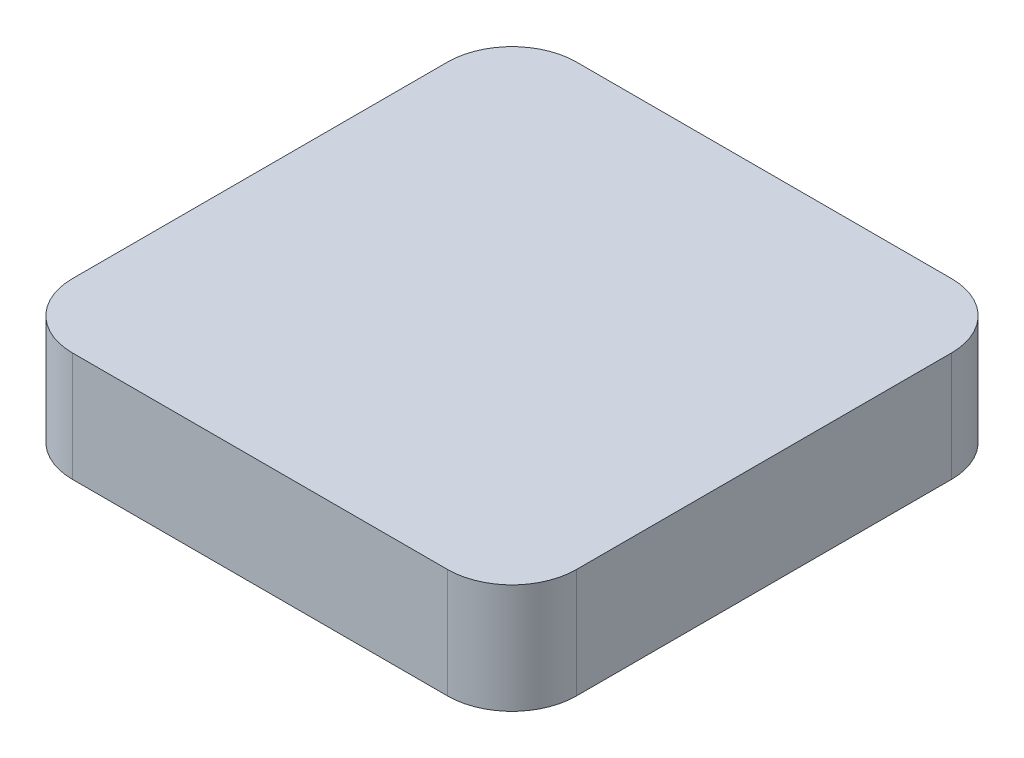
SolidWorks part; units mm, degrees
ref_plane "前视基准面" through (0, 0, 0) normal (0, 0, 1) x (1, 0, 0)
ref_plane "上视基准面" through (0, 0, 0) normal (0, 1, 0) x (1, 0, 0)
ref_plane "右视基准面" through (0, 0, 0) normal (1, 0, 0) x (0, 0, -1)
sketch "草图1" plane through (0, 0, 0) normal (0, 1, 0) x (1, 0, 0)
  line L1 (-28.9073, 18.1297) -> (10.1927, 18.1297)
  line L2 (-28.9073, 18.1297) -> (-28.9073, -20.9703)
  line L3 (-28.9073, -20.9703) -> (10.1927, -20.9703)
  line L4 (10.1927, 18.1297) -> (10.1927, -20.9703)
  line L5 (-28.9073, 18.1297) -> (10.1927, -20.9703) construction
  line L6 (-28.9073, -20.9703) -> (10.1927, 18.1297) construction
  point P0 (-9.3573, -1.4203)
  dimension "D1" = 39.1
  dimension "D2" = 39.1
extrude "凸台-拉伸1" add sketch "草图1" along normal blind 8.5
fillet "圆角1" radius 5 4 edges at (10.1927, 4.25, -18.1297) (10.1927, 4.25, 20.9703) (-28.9073, 4.25, 20.9703) (-28.9073, 4.25, -18.1297)
